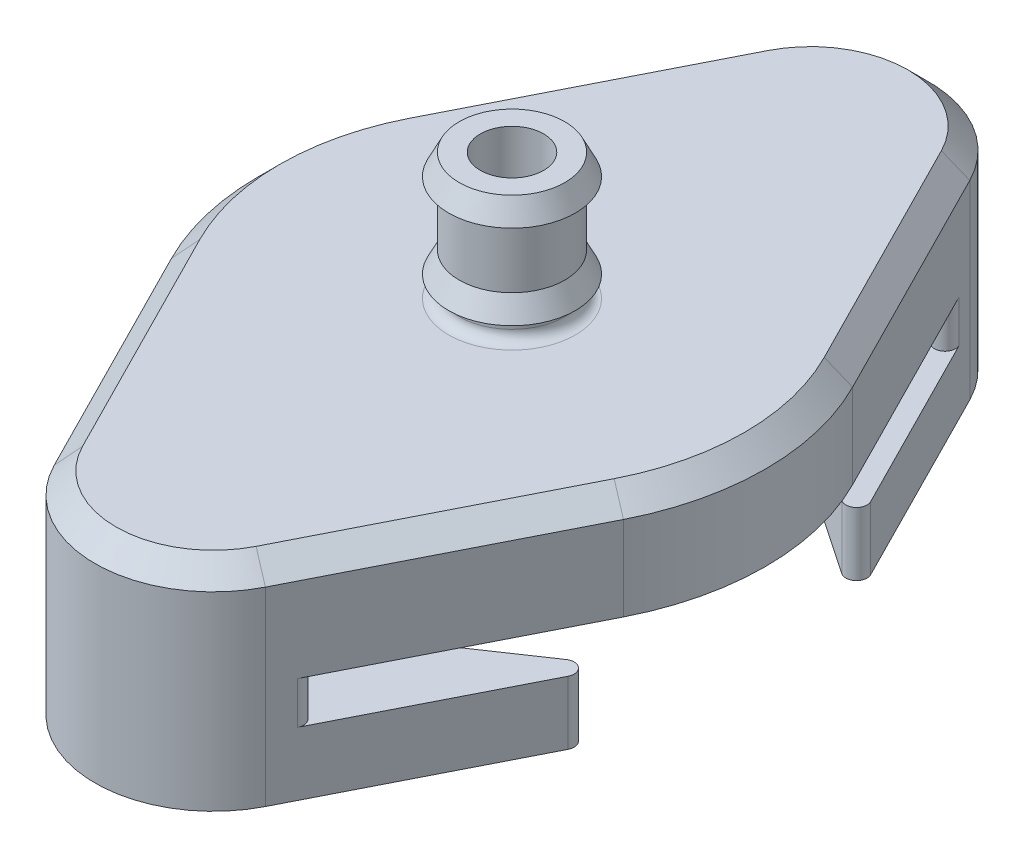
SolidWorks part; units mm, degrees
ref_plane "Front Plane" through (0, 0, 0) normal (0, 0, 1) x (1, 0, 0)
ref_plane "Top Plane" through (0, 0, 0) normal (0, 1, 0) x (1, 0, 0)
ref_plane "Right Plane" through (0, 0, 0) normal (1, 0, 0) x (0, 0, -1)
sketch "Sketch2" plane through (0, 0, 0) normal (1, 0, 0) x (0, 0, -1)
  line L0 (-1.5, 0) -> (0, 0) construction
  line L5 (-2.5, 0) -> (-19.75, 0)
  line L7 (-1.5, -5) -> (-15.75, -5)
  line L8 (-19.75, 0) -> (-19.75, -10)
  line L11 (-19.75, -10) -> (-8.75, -10)
  line L12 (-15.75, -5) -> (-15.75, -7)
  line L15 (-15.75, -7) -> (-8.75, -7)
  line L16 (-8.75, -10) -> (-8.75, -7)
  line L17 (-1.5, 6) -> (-1.5, -5)
  line L19 (-2.5, 0) -> (-2.5, 1)
  line L20 (-2.5, 6) -> (-1.5, 6)
  line L22 (-2.5, 6) -> (-3, 5)
  line L23 (-3, 5) -> (-2.5, 5)
  line L24 (-2.5, 2) -> (-3, 1)
  line L25 (-3, 1) -> (-2.5, 1)
  line L26 (-2.5, 2) -> (-2.5, 5)
  line L37 (0, 7.88) -> (0, -7.88) construction
  dimension "D2" = 2
  dimension "D3" = 4
  dimension "D4" = 3
  dimension "D1" = 15.75
  dimension "D5" = 0.5
  dimension "D8" = 1
  dimension "D9" = 1
  dimension "D10" = 3
  dimension "D15" = 8.75
  dimension "D6" = 2.5
  dimension "D7" = 1
  dimension "D11" = 1
  dimension "D12" = 5
revolve "Revolve1" add sketch "Sketch2" angle 360 about L37
sketch "Sketch3" plane through (0, 0, 0) normal (0, 1, 0) x (1, 0, 0)
  line L0 (-10.7037, 5.425) -> (-5, 16.6786)
  line L1 (5, 16.6786) -> (10.7037, 5.425)
  line L2 (-10.7037, -5.425) -> (-5, -16.6786)
  line L3 (5, -16.6786) -> (10.7037, -5.425)
  line L4 (0, 14.1445) -> (0, -14.1445) construction
  arc A0 (-10.7037, -5.425) -> (-10.7037, 5.425) centre (0, 0) cw
  arc A1 (10.7037, 5.425) -> (10.7037, -5.425) centre (0, 0) cw
  arc A2 (-5, 16.6786) -> (5, 16.6786) centre (0, 14.1445) cw
  arc A3 (-5, -16.6786) -> (5, -16.6786) centre (0, -14.1445) ccw
  circle A4 centre (0, 0) radius 19.75 construction
  circle A10 centre (0, 0) radius 19.75
  point P12 (0, 0)
  circle M11 centre (0, 0) radius 19.75
  dimension "D1" = 12
  dimension "D2" = 12
  dimension "D4" = 5
extrude "Cut-Extrude1" cut sketch "Sketch3" against normal through all contours A3 L2 A0 L0 A2 M11 | A3 A2 L1 A1 L3 M11
sketch "Sketch5" plane through (0, -10, 0) normal (0, -1, 0) x (1, 0, 0)
  line L0 (-5.8847, -8.696) -> (-11.3463, -5)
  line L1 (-11.3463, 5) -> (-5.8847, 8.696)
  line L2 (5.8847, 8.696) -> (11.3463, 5)
  line L3 (11.3463, -5) -> (5.8847, -8.696)
  line L4 (-7.9627, 0) -> (7.9627, 0) construction
  arc A0 (5.8847, -8.696) -> (-5.8847, -8.696) centre (0, 0) cw
  arc A1 (-11.3463, -5) -> (-11.3463, 5) centre (-7.9627, 0) cw
  arc A2 (-5.8847, 8.696) -> (5.8847, 8.696) centre (0, 0) cw
  arc A3 (11.3463, 5) -> (11.3463, -5) centre (7.9627, 0) cw
  circle A12 centre (0, 0) radius 14 construction
  point P12 (0, 0)
  dimension "D1" = 10.5
  dimension "D2" = 28
  dimension "D3" = 10.5
  dimension "D4" = 5
extrude "Cut-Extrude3" cut sketch "Sketch5" against normal up to surface (5 mm away) up to face at (0, -5, 1.5)
fillet "Fillet1" radius 0.5 8 edges at (-6.092, -6, 14.5241) (6.092, -6, -14.5241) (-6.092, -6, -14.5241) (6.092, -6, 14.5241) (-10.6961, -8.5, -5.44) (10.6961, -8.5, -5.44) (-10.6961, -8.5, 5.44) (10.6961, -8.5, 5.44)
fillet "Fillet3" radius 0.5 1 edges at (0, 0, 2.5)
sketch "Sketch11" plane through (0, 0, 0) normal (1, 0, 0) x (0, 0, -1)
  line L1 (-17.0456, -1.5) -> (17.0456, -1.5)
  line L2 (-17.0456, -1.5) -> (-17.0456, -15.1462)
  line L3 (-17.0456, -15.1462) -> (17.0456, -15.1462)
  line L4 (17.0456, -1.5) -> (17.0456, -15.1462)
  line L5 (-17.0456, -1.5) -> (17.0456, -15.1462) construction
  line L6 (-17.0456, -15.1462) -> (17.0456, -1.5) construction
  point P0 (0, -8.3231)
  dimension "D1" = 1.5
extrude "Cut-Extrude6" [suppressed] cut sketch "Sketch11" against normal through all both and the other way through all
chamfer "Chamfer2" distance 1 angle 45 8 edges at (-7.8519, 0, -11.0518) (-12, 0, 0) (0, 0, -19.75) (-7.8519, 0, 11.0518) (7.8519, 0, -11.0518) (0, 0, 19.75) (12, 0, 0) (7.8519, 0, 11.0518)
sketch "Sketch12" plane through (0, -10, 0) normal (0, -1, 0) x (1, 0, 0)
  line L0 (0, 19.75) -> (0, -19.75) construction
  arc A0 (5, 16.6786) -> (-5, 16.6786) centre (0, 14.1445) ccw construction
  arc A1 (-5, -16.6786) -> (5, -16.6786) centre (0, -14.1445) ccw construction
  circle A2 centre (0, -13.25) radius 1.4
  circle A3 centre (0, 13.25) radius 1.4
  dimension "D1" = 2.8
  dimension "D2" = 2.8
  dimension "D3" = 6.5
  dimension "D4" = 6.5
extrude "Cut-Extrude7" cut sketch "Sketch12" against normal up to surface (5 mm away) up to face at (0, -5, 0)
equation "\"syringeOuterRadius\"= 31"
equation "\"syringeTubeRadius\"= 17"
equation "\"syringeTubeInnerRadius\"= 15"
equation "\"D1@Sketch2\"=(\"syringeOuterRadius\"+0.5)/2"
